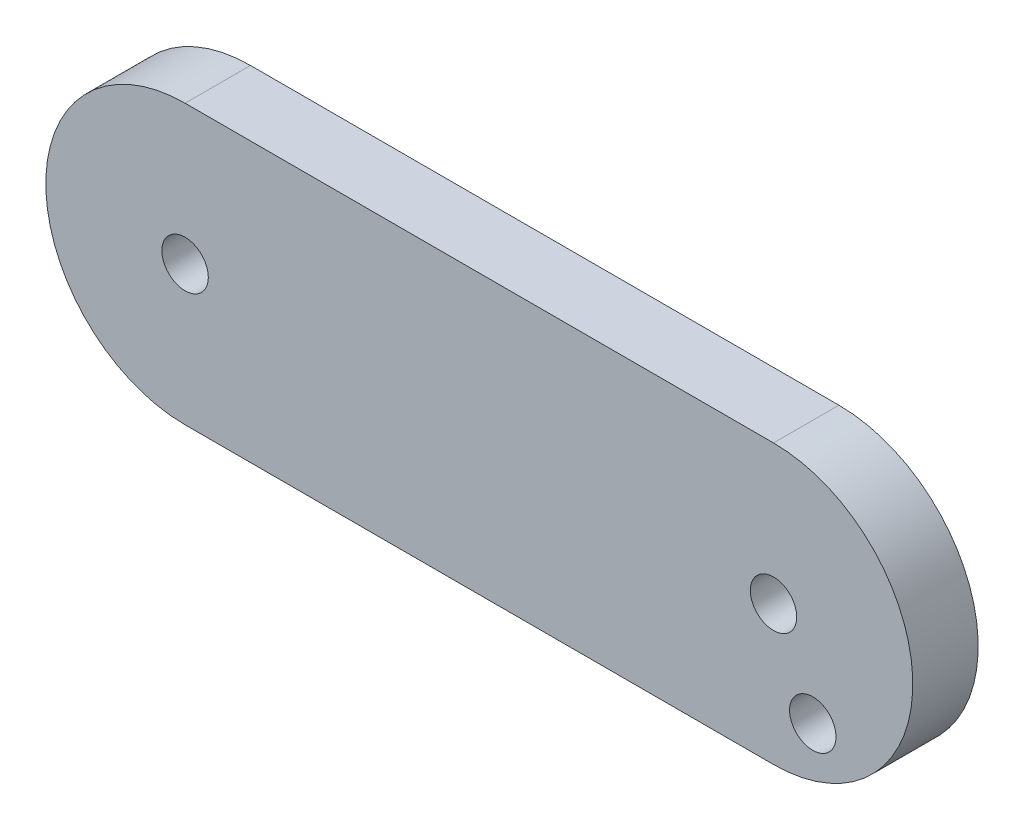
SolidWorks part; units mm, degrees
ref_plane "Front Plane" through (0, 0, 0) normal (0, 0, 1) x (1, 0, 0)
ref_plane "Top Plane" through (0, 0, 0) normal (0, 1, 0) x (1, 0, 0)
ref_plane "Right Plane" through (0, 0, 0) normal (1, 0, 0) x (0, 0, -1)
sketch "Sketch1" plane through (-36.5352, -38.2846, 568.0193) normal (0, 0, 1) x (1, 0, 0)
  line L0 (36.5352, 38.2846) -> (14.0352, 38.2846) construction
  line L1 (14.0352, 38.2846) -> (36.5352, 38.2846) construction
  line L2 (14.0352, 43.6096) -> (36.5352, 43.6096)
  line L3 (14.0352, 32.9596) -> (36.5352, 32.9596)
  circle A0 centre (36.5352, 38.2846) radius 0.8875
  circle A1 centre (14.0352, 38.2846) radius 0.8875
  arc A2 (14.0352, 43.6096) -> (14.0352, 32.9596) centre (14.0352, 38.2846) ccw
  arc A3 (36.5352, 32.9596) -> (36.5352, 43.6096) centre (36.5352, 38.2846) ccw
  point P3 (25.2852, 38.2846)
  dimension "D1" = 1.775
  dimension "D4" = 5.325
  dimension "D3" = 22.5
  dimension "D2" = 2
extrude "Boss-Extrude1" add sketch "Sketch1" along normal blind 2.5 contours L2 A3 L3 A2
sketch "Sketch3" plane through (0, 0, 568.0193) normal (0, 0, -1) x (-1, 0, 0)
  circle A0 centre (-1.501, -3.2171) radius 0.8875 construction
  circle A1 centre (-1.501, -3.2171) radius 0.8875
extrude "Cut-Extrude2" cut sketch "Sketch3" against normal through all
equation "\"filamentDia\"=1.775"
equation "\"D1@Sketch1\"=\"filamentDia\""
